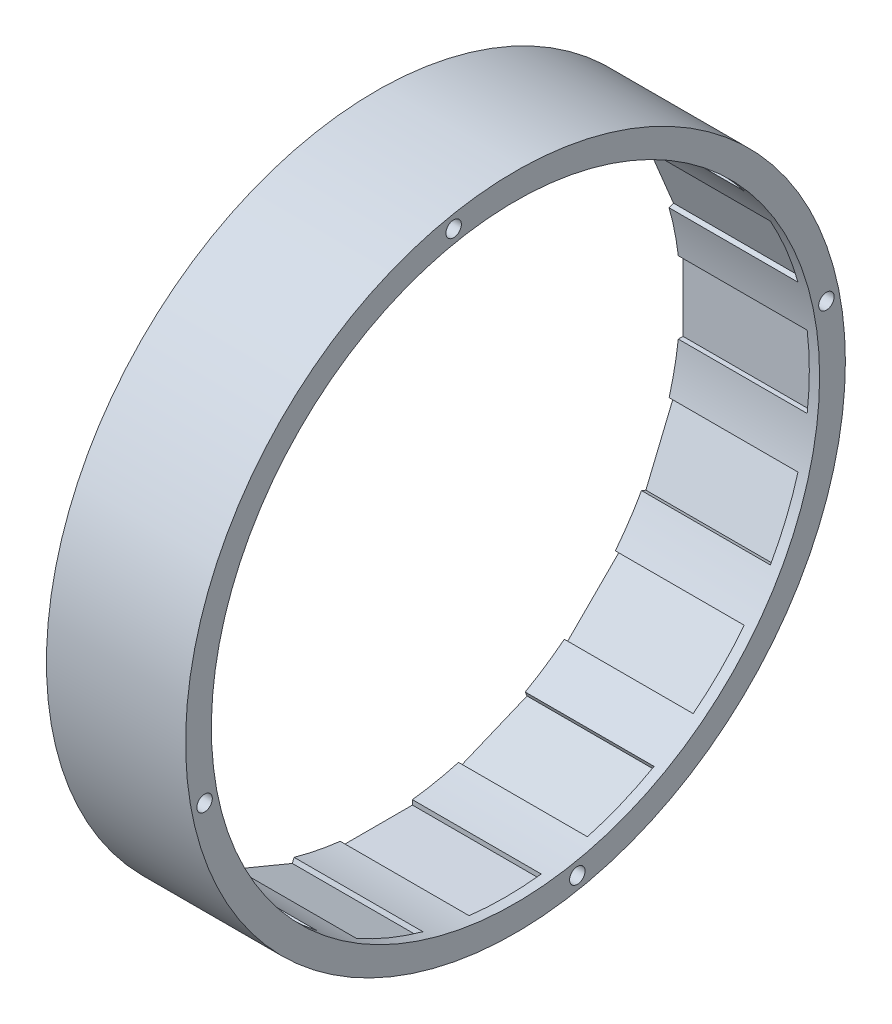
SolidWorks part; units mm, degrees
material "1060-H12"
ref_plane "Front Plane" through (0, 0, 0) normal (0, 0, 1) x (1, 0, 0)
ref_plane "Top Plane" through (0, 0, 0) normal (0, 1, 0) x (1, 0, 0)
ref_plane "Right Plane" through (0, 0, 0) normal (1, 0, 0) x (0, 0, -1)
sketch "Sketch1" plane through (0, 0, 0) normal (1, 0, 0) x (0, 0, -1)
  circle A0 centre (0, 0) radius 64
  circle A1 centre (0, 0) radius 59
  dimension "D1" = 128
  dimension "D2" = 118
extrude "Boss-Extrude1" add sketch "Sketch1" along normal blind 27
sketch "Sketch2" plane through (0, 0, 0) normal (-1, 0, 0) x (0, 0, 1)
  line L1 (7, 0) -> (-7, 0)
  line L2 (7, 0) -> (7, 59.5)
  line L3 (7, 59.5) -> (-7, 59.5)
  line L4 (-7, 0) -> (-7, 59.5)
  circle A1 centre (0, 0) radius 59 construction
  point P4 (0, 0)
  point P5 (0, 59.5)
  dimension "D1" = 14
  dimension "D2" = 0.5
extrude "Cut-Extrude1" cut sketch "Sketch2" against normal blind 25
pattern_circular "CirPattern1" count 16 over 360 about axis through (0, 0, 0) along (1, 0, 0) of "Cut-Extrude1"
sketch "Sketch3" plane through (0, 0, 0) normal (-1, 0, 0) x (0, 0, 1)
  line L0 (0, 0) -> (11.9981, 60.3183) construction
  arc A0 (15.9517, 56.8027) -> (7, 58.5833) centre (0, 0) ccw construction
  circle A1 centre (11.9981, 60.3183) radius 1.5
  point P7 (11.5103, 57.8663)
  dimension "D2" = 3
  dimension "D1" = 61.5
extrude "Cut-Extrude2" cut sketch "Sketch3" against normal through all
pattern_circular "CirPattern2" count 4 over 360 about axis through (0, 0, 0) along (1, 0, 0) of "Cut-Extrude2"
